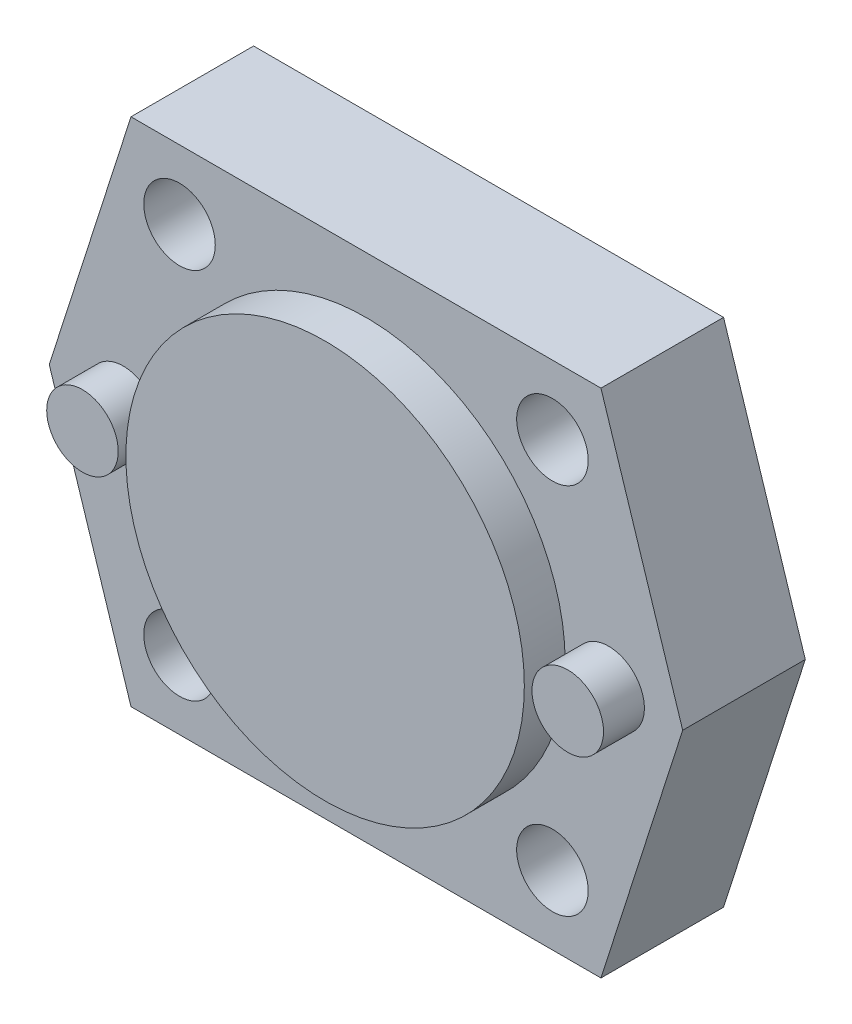
SolidWorks part; units mm, degrees
ref_plane "Front Plane" through (0, 0, 0) normal (0, 0, 1) x (1, 0, 0)
ref_plane "Top Plane" through (0, 0, 0) normal (0, 1, 0) x (1, 0, 0)
ref_plane "Right Plane" through (0, 0, 0) normal (1, 0, 0) x (0, 0, -1)
sketch "Sketch1" plane through (0, 0, 0) normal (0, 0, 1) x (1, 0, 0)
  line L0 (-23, 25) -> (23, 25)
  line L1 (23, 25) -> (31, 0)
  line L2 (31, 0) -> (23, -25)
  line L3 (23, -25) -> (-23, -25)
  line L4 (-23, -25) -> (-31, 0)
  line L5 (-31, 0) -> (-23, 25)
  line L6 (-31, 0) -> (31, 0) construction
  line L7 (0, 25) -> (0, -25) construction
  line L8 (-23, 25) -> (-23, -25) construction
  line L9 (23, -25) -> (23, 25) construction
  point P8 (0, 0)
  point P10 (0, 0)
  dimension "D1" = 50
  dimension "D2" = 62
  dimension "D3" = 46
extrude "Boss-Extrude1" add sketch "Sketch1" along normal blind 12
sketch "Sketch2" plane through (0, 0, 12) normal (0, 0, 1) x (1, 0, 0)
  line L0 (-31, 0) -> (31, 0) construction
  circle A0 centre (0, 0) radius 19.5
  circle A1 centre (23.75, 0) radius 3.5
  circle A2 centre (-23.75, 0) radius 3.5
  dimension "D1" = 39
  dimension "D2" = 7
  dimension "D3" = 23.75
  dimension "D4" = 23.75
extrude "Boss-Extrude2" add sketch "Sketch2" along normal blind 4
fillet "Fillet1" [suppressed] radius 2
sketch "Sketch3" plane through (0, 0, 12) normal (0, 0, 1) x (1, 0, 0)
  line L1 (-18.25, -18.25) -> (18.25, -18.25) construction
  line L2 (-18.25, -18.25) -> (-18.25, 18.25) construction
  line L3 (-18.25, 18.25) -> (18.25, 18.25) construction
  line L4 (18.25, -18.25) -> (18.25, 18.25) construction
  line L5 (-18.25, -18.25) -> (18.25, 18.25) construction
  line L6 (-18.25, 18.25) -> (18.25, -18.25) construction
  circle A0 centre (18.25, 18.25) radius 3.5
  circle A1 centre (18.25, -18.25) radius 3.5
  circle A2 centre (-18.25, -18.25) radius 3.5
  circle A3 centre (-18.25, 18.25) radius 3.5
  circle A4 centre (0, 0) radius 25.8094 construction
  point P0 (0, 0)
  dimension "D3" = 7
  dimension "D4" = 51.6188
  dimension "D1" = 36.5
  dimension "D2" = 36.5
extrude "Cut-Extrude1" cut sketch "Sketch3" against normal blind 12
